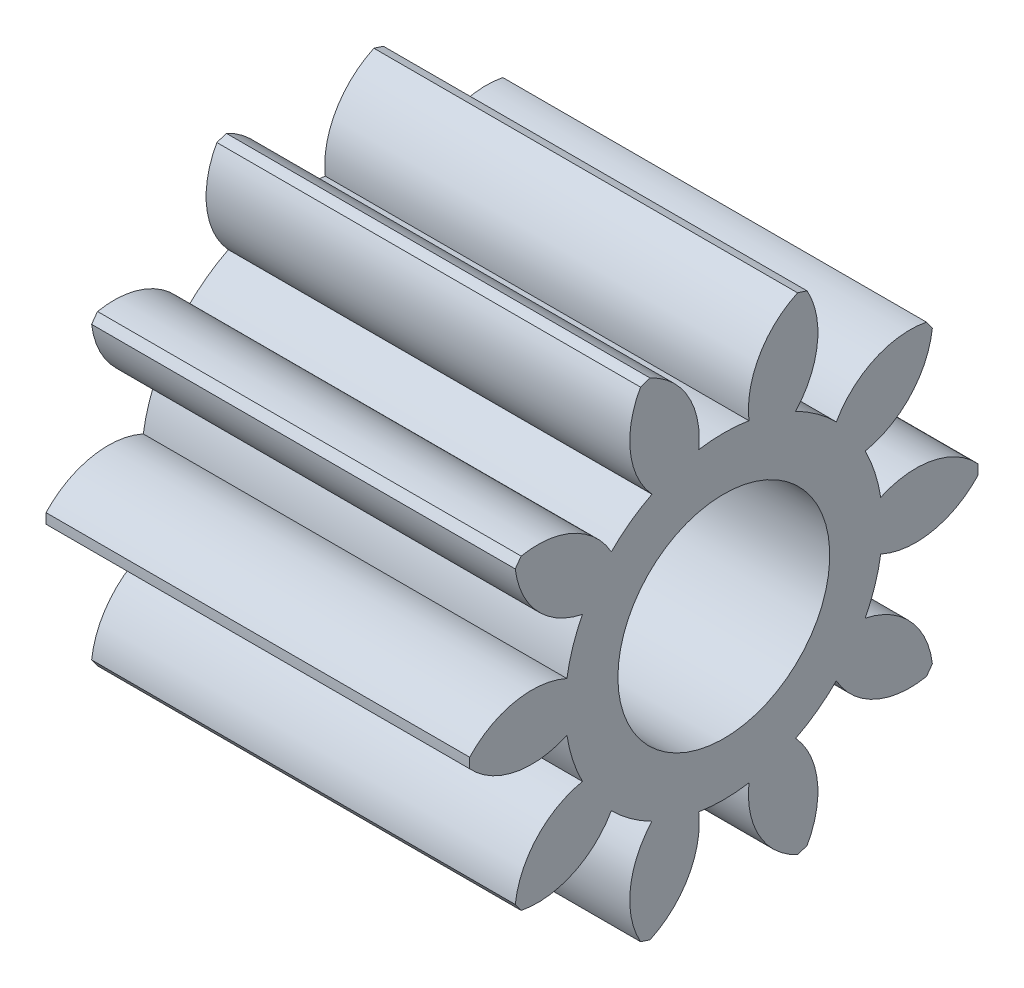
SolidWorks part; units mm, degrees
ref_plane "Plane1" through (0, 0, 0) normal (0, 0, 1) x (1, 0, 0)
ref_plane "Plane2" through (0, 0, 0) normal (0, 1, 0) x (1, 0, 0)
ref_plane "Plane3" through (0, 0, 0) normal (1, 0, 0) x (0, 0, -1)
other "Configuration Table"
sketch "HoldingSke" plane through (0, 0, 0) normal (0, 1, 0) x (1, 0, 0)
  line L0 (0, 0) -> (0.9848, -0.1736)
  line L1 (-15, 0) -> (100, 0) construction
  line L2 (0, 0) -> (-2.1039, 2.3779)
  line L3 (0, 0) -> (-11.863, 4.5341)
  line L4 (0, 0) -> (8.5048, 1.4996)
  line L5 (0, 0) -> (-46.8476, -17.4728)
  line L6 (0, 0) -> (-8.2896, -5.593)
  line L7 (-2.1039, 2.3779) -> (8.6586, 51.2059)
  line L8 (-76.2, 54.61) -> (-75.3, 54.61)
  line L9 (-71.009, 38.7566) -> (-53.1078, 45.2721)
  line L10 (-76.2, 71.12) -> (104.1128, 71.12)
  line L11 (0, 0) -> (-10, 0)
  line L12 (-76.2, 101.6) -> (-76.162, 101.6)
  line L13 (24.9733, 27.94) -> (52.9518, 28.4284)
  line L14 (24.9733, 27.94) -> (24.9743, 27.94)
  line L15 (24.9733, 27.94) -> (100.4006, 29.5858)
  line L16 (-63.627, -1) -> (-12.827, -1)
  circle A0 centre (0, 0) radius 2.5
  circle A1 centre (0, 0) radius 3.749
  circle A2 centre (0, 0) radius 37.5
  circle A3 centre (0, 0) radius 2.5
  dimension "MHD" = 7.498
  dimension "Hub_dia" = 75
  dimension "Bore" = 5
  dimension "MBD" = 5
  dimension "Num_teeth" = 10
  dimension "Pitch" = 1
  dimension "Overall_len" = 50
  dimension "Show_teeth" = 10
  dimension "Thickness" = 10
  dimension "OAL" = 50.0001
  dimension "T_dim" = 0.9
  dimension "Ap" = 20
  dimension "H" = 19.05
  dimension "Pitch_radius" = 180.3128
  dimension "Width" = 10
  dimension "Backlash" = 0.038
  dimension "Addendum_fac" = 1
  dimension "Dedendum_fac" = 1.25
  dimension "Clearance_fac" = 0.25
  dimension "Dedendum_add" = 0.001
  dimension "Module" = 1
sketch "BasProSke" plane through (0, 0, 0) normal (0, 1, 0) x (1, 0, 0)
  line L0 (-10, 0) -> (60, 0) construction
  line L1 (0, 0) -> (0, 6)
  line L2 (0, 0) -> (10, 0)
  line L3 (10, 0) -> (10, 6)
  line L4 (10, 6) -> (0, 6)
  dimension "Thickness" = 10
  dimension "Diameter" = 12
revolve "Base-Revolve" add sketch "BasProSke" angle 360 about L0
sketch "TooCutSke" plane through (0, 0, 0) normal (1, 0, 0) x (0, 0, -1)
  line L1 (0, 0) -> (0, 107) construction
  line L2 (0, 0) -> (-0.8485, 4.9275) construction
  line L3 (0, 0) -> (-3.0584, 9.4126) construction
  line L4 (-0.8485, 4.9275) -> (-1.5292, 4.7063) construction
  arc A0 (0.5928, 3.7018) -> (-0.5928, 3.7018) centre (0, 0) ccw
  arc A1 (1.7758, 5.7578) -> (-1.7758, 5.7578) centre (0, 0) ccw
  circle A2 centre (0, 0) radius 5 construction
  circle A3 centre (0, 0) radius 4.6985 construction
  arc A4 (-0.5928, 3.7018) -> (-1.7758, 5.7578) centre (-2.5801, 3.9267) ccw
  arc A5 (1.7758, 5.7578) -> (0.5928, 3.7018) centre (2.5801, 3.9267) ccw
  dimension "Root_dia" = 7.498
  dimension "Overcut_dia" = 12.0508
  dimension "Pitch_dia" = 10
  dimension "Base_dia" = 9.3969
  dimension "Flank_rad" = 2
  dimension "Half_ang" = 18
  dimension "Half_CT" = 0.7157
extrude "ToothCut" cut sketch "TooCutSke" along normal through all
fillet "Breaks" [suppressed] radius 0.02
fillet "RootFillets" [suppressed] radius 0.251
pattern_circular "TeethCuts" count 10 every 36 about axis through (-10, 0, 0) along (1, 0, 0) of "ToothCut", "RootFillets", "Breaks"
sketch "HubNeaOneSke" plane through (0, 0, 0) normal (-1, 0, 0) x (0, 0, 1)
  circle A0 centre (0, 0) radius 3.749
  dimension "Diameter" = 7.498
extrude "HubNearOne" [suppressed] add sketch "HubNeaOneSke" along normal blind 40.0001
sketch "HubNeaBotSke" plane through (0, 0, 0) normal (-1, 0, 0) x (0, 0, 1)
  circle A0 centre (0, 0) radius 3.749
  dimension "Diameter" = 7.498
extrude "HubNearBoth" [suppressed] add sketch "HubNeaBotSke" along normal blind 20
ref_plane "FarPln" through (10, 0, 0) normal (1, 0, 0) x (0, 0, -1)
sketch "HubFarSke" plane through (10, 0, 0) normal (1, 0, 0) x (0, 0, -1)
  circle A0 centre (0, 0) radius 3.749
  dimension "Diameter" = 7.498
extrude "HubFar" [suppressed] add sketch "HubFarSke" along normal blind 20
sketch "BorSke" plane through (0, 0, 0) normal (1, 0, 0) x (0, 0, -1)
  circle A0 centre (0, 0) radius 2.5
  dimension "Diameter" = 5
extrude "Bore" cut sketch "BorSke" along normal mid plane 100.0001
sketch "KeySke" plane through (0, 0, 0) normal (1, 0, 0) x (0, 0, -1)
  line L0 (-1, 0) -> (-1, 3.4)
  line L1 (-1, 3.4) -> (1, 3.4)
  line L2 (1, 3.4) -> (1, 0)
  line L3 (0, 0) -> (0, 34) construction
  line L4 (-1, 0) -> (1, 0)
  dimension "Offset" = 3.4
  dimension "Width" = 2
extrude "Keyway" [suppressed] cut sketch "KeySke" along normal mid plane 100.0001
pattern_circular "Keyway2" [suppressed] count 2 every 90 about axis through (-10, 0, 0) along (1, 0, 0)
equation "' \"Module@HoldingSke\" = 6.35"
equation "' \"Num_teeth@HoldingSke\" = 12"
equation "' \"Ap@HoldingSke\" =  20"
equation "' \"Ap@HoldingSke\" = 20"
equation "' \"Width@HoldingSke\" = 0.5 * 25.4"
equation "' \"Hub_dia@HoldingSke\"= 1 * 25.4"
equation "' \"Hub_dia@HoldingSke\" = 1 * 25.4"
equation "' \"Overall_len@HoldingSke\" = 1.0 * 25.4"
equation "' \"Bore@HoldingSke\" = 0.75 * 25.4"
equation "' \"T_dim@HoldingSke\" = 0.1 * 25.4"
equation "' \"Width@KeySke\" = 0.25 * 25.4"
equation "' \"Show_teeth@HoldingSke\" = 13"
equation "' \"Backlash@HoldingSke\" = 0.009 * 25.4"
equation "' \"Addendum_fac@HoldingSke\" = 1.0"
equation "' \"Dedendum_fac@HoldingSke\" = 1.25"
equation "' \"Dedendum_add@HoldingSke\" = 0.00005 * 25.4"
equation "' \"Clearance_fac@HoldingSke\" = 0.25"
equation "\"Pitch@HoldingSke\" = 1 / \"Module@HoldingSke\""
equation "\"Overcut_dia@TooCutSke\" = (\"Num_teeth@HoldingSke\" + 2 * \"Addendum_fac@HoldingSke\") / \"Pitch@HoldingSke\" + 0.002 * 25.4"
equation "\"Pitch_dia@TooCutSke\" = \"Num_teeth@HoldingSke\" / \"Pitch@HoldingSke\""
equation "\"Base_dia@TooCutSke\" = \"Num_teeth@HoldingSke\" / \"Pitch@HoldingSke\" * cos((\"Ap@HoldingSke\"  * 3.14159265 / 180))"
equation "\"Root_dia@TooCutSke\" = (\"Num_teeth@HoldingSke\" + 2) / \"Pitch@HoldingSke\" - 2 * (\"Addendum_fac@HoldingSke\" + \"Dedendum_fac@HoldingSke\") / \"Pitch@HoldingSke\" - \"Dedendum_add@HoldingSke\" * 2"
equation "\"Half_ang@TooCutSke\" = 180 / \"Num_teeth@HoldingSke\""
equation "\"Half_CT@TooCutSke\" = \"Num_teeth@HoldingSke\" / \"Pitch@HoldingSke\" * sin((3.14159265 / 2 / \"Num_teeth@HoldingSke\")) / 2 - 7 * \"Backlash@HoldingSke\" / 4"
equation "\"Flank_rad@TooCutSke\" = \"Num_teeth@HoldingSke\" / \"Pitch@HoldingSke\" / 5"
equation "\"Radius@RootFillets\" = \"Clearance_fac@HoldingSke\" / \"Pitch@HoldingSke\" + \"Dedendum_add@HoldingSke\""
equation "\"Break_rad@Breaks\" = 0.02 / \"Pitch@HoldingSke\""
equation "\"Thickness@HoldingSke\" = \"Width@HoldingSke\""
equation "\"OAL@HoldingSke\" = \"Thickness@HoldingSke\""
equation "\"MHD@HoldingSke\" = (\"Num_teeth@HoldingSke\" + 2) / \"Pitch@HoldingSke\" - 2 * (\"Addendum_fac@HoldingSke\" + \"Dedendum_fac@HoldingSke\")  / \"Pitch@HoldingSke\" - \"Dedendum_add@HoldingSke\" * 2"
equation "\"MBD@HoldingSke\" = (\"Num_teeth@HoldingSke\" + 2) / \"Pitch@HoldingSke\" - 2 * (\"Addendum_fac@HoldingSke\" + \"Dedendum_fac@HoldingSke\")  / \"Pitch@HoldingSke\" - \"Dedendum_add@HoldingSke\" * 2 - 0.002 * 25.4"
equation "\"MHD@HoldingSke\" = ((sgn( \"MHD@HoldingSke\" - \"Hub_dia@HoldingSke\" )-1)*( \"MHD@HoldingSke\" - \"Hub_dia@HoldingSke\" ))/-2+ \"Hub_dia@HoldingSke\""
equation "\"MBD@HoldingSke\" = ((sgn( \"MBD@HoldingSke\" - \"Bore@HoldingSke\" )-1)*( \"MBD@HoldingSke\" - \"Bore@HoldingSke\" ))/-2+ \"Bore@HoldingSke\""
equation "\"OAL@HoldingSke\" = ((sgn( \"OAL@HoldingSke\" - \"Overall_len@HoldingSke\" )+1)*( \"OAL@HoldingSke\" - \"Overall_len@HoldingSke\" ))/2 + \"Overall_len@HoldingSke\" + 0.000002 * 25.4"
equation "\"Num_teeth@TeethCuts\" = int( \"Show_teeth@HoldingSke\" ) + 1"
equation "\"Num_teeth@TeethCuts\" = ((sgn( \"Num_teeth@TeethCuts\" - \"Num_teeth@HoldingSke\" )-1)*( \"Num_teeth@TeethCuts\" - \"Num_teeth@HoldingSke\" ))/-2+ \"Num_teeth@HoldingSke\""
equation "\"Num_teeth@TeethCuts\" = ((sgn( \"Num_teeth@TeethCuts\" - 2.0)+1)*( \"Num_teeth@TeethCuts\" - 2.0))/2 +2.0"
equation "\"Angle@TeethCuts\" = 360.0 / \"Num_teeth@HoldingSke\""
equation "\"Diameter@BasProSke\" = (\"Num_teeth@HoldingSke\" + 2 * \"Addendum_fac@HoldingSke\") / \"Pitch@HoldingSke\""
equation "\"Thickness@BasProSke\"  = \"Thickness@HoldingSke\""
equation "' \"Fillet_rad@BasProSke\" =  \"Thickness@HoldingSke\" * 0.05"
equation "' \"Fillet_rad@BasProSke\" = \"Thickness@HoldingSke\" * 0.05"
equation "\"MHD@HoldingSke\" = ((sgn( \"MHD@HoldingSke\" - \"Root_dia@TooCutSke\" )-1)*( \"MHD@HoldingSke\" - \"Root_dia@TooCutSke\" ))/-2+ \"Root_dia@TooCutSke\""
equation "\"Diameter@HubNeaOneSke\" = \"MHD@HoldingSke\""
equation "\"Length@HubNearOne\" = \"OAL@HoldingSke\" - \"Thickness@BasProSke\""
equation "\"Diameter@HubNeaBotSke\" = \"MHD@HoldingSke\""
equation "\"Length@HubNearBoth\" = ( \"OAL@HoldingSke\" - \"Thickness@BasProSke\" ) / 2.0"
equation "\"Thickness@FarPln\" = \"Thickness@BasProSke\""
equation "\"Diameter@HubFarSke\" = \"MHD@HoldingSke\""
equation "\"Length@HubFar\" = ( \"OAL@HoldingSke\" - \"Thickness@BasProSke\" ) / 2.0"
equation "\"Diameter@BorSke\" = \"MBD@HoldingSke\""
equation "\"D1@Bore\" = \"OAL@HoldingSke\" * 2.0"
equation "\"D1@Keyway\" = \"OAL@HoldingSke\" * 2.0"
equation "\"Offset@KeySke\" = \"T_dim@HoldingSke\" + \"MBD@HoldingSke\" / 2.0"
